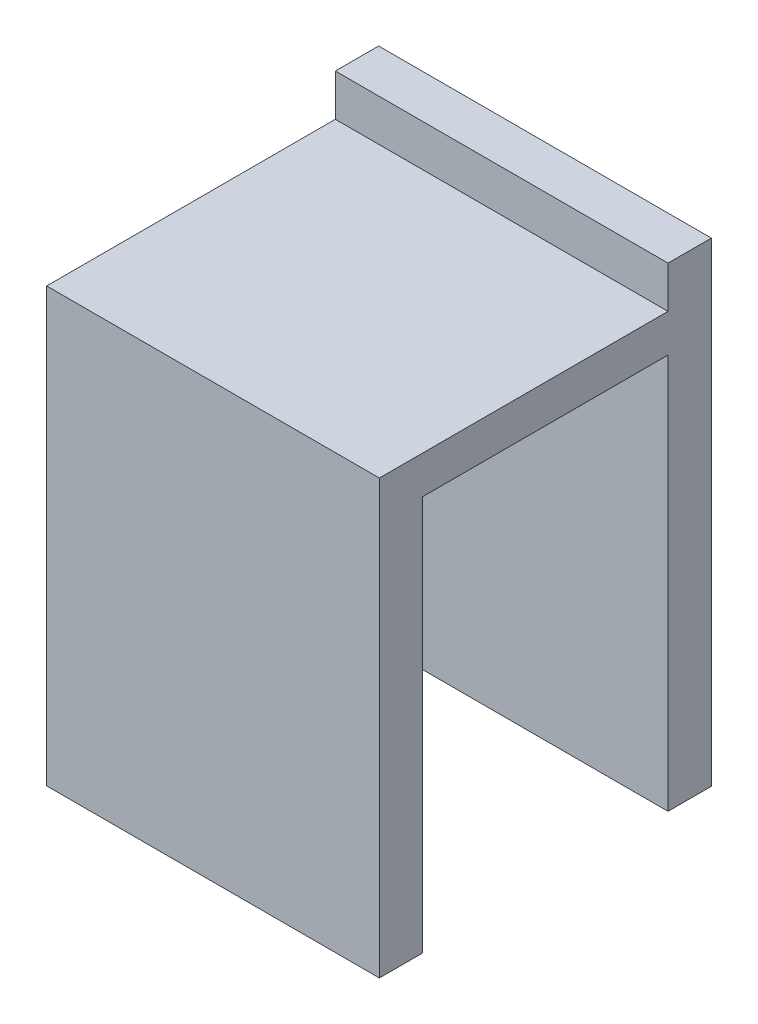
SolidWorks part; units mm, degrees
ref_plane "Front Plane" through (0, 0, 0) normal (0, 0, 1) x (1, 0, 0)
ref_plane "Top Plane" through (0, 0, 0) normal (0, 1, 0) x (1, 0, 0)
ref_plane "Right Plane" through (0, 0, 0) normal (1, 0, 0) x (0, 0, -1)
sketch "Sketch2" plane through (0, 0, -200) normal (0, 0, -1) x (-1, 0, 0)
  line L1 (91.2408, 47.6545) -> (91.2408, 22.1545) construction
  line L3 (91.2408, 22.1545) -> (91.2408, -7.8455)
  line L4 (91.2408, -7.8455) -> (68.1888, -7.8455)
  line L5 (68.1888, 22.1545) -> (68.1888, -7.8455)
  line L7 (68.1888, 22.1545) -> (68.1888, 25.0516)
  line L8 (68.1888, 25.0516) -> (91.2408, 25.0516)
  line L9 (91.2408, 22.1545) -> (91.2408, 25.0516)
  dimension "D1" = 30
extrude "Boss-Extrude1" add sketch "Sketch2" along normal blind 3
sketch "Sketch3" plane through (0, 0, -200) normal (0, 0, 1) x (1, 0, 0)
  line L0 (-91.2408, -7.8455) -> (-91.2408, 25.0516) construction
  line L1 (-91.2408, 19.5359) -> (-68.1888, 19.5359)
  line L2 (-91.2408, 19.5359) -> (-91.2408, 22.1545)
  line L3 (-91.2408, 22.1545) -> (-68.1888, 22.1545)
  line L4 (-68.1888, 19.5359) -> (-68.1888, 22.1545)
  line L5 (-68.1888, 25.0516) -> (-68.1888, -7.8455) construction
  line L6 (41.6818, 22.1545) -> (-91.2408, 22.1545) construction
extrude "Boss-Extrude2" add sketch "Sketch3" along normal blind 20
sketch "Sketch5" plane through (0, 0, -180) normal (0, 0, 1) x (1, 0, 0)
  line L1 (-91.2408, 19.5359) -> (-68.1888, 19.5359)
  line L2 (-91.2408, 19.5359) -> (-91.2408, -7.8455)
  line L3 (-91.2408, -7.8455) -> (-68.1888, -7.8455)
  line L4 (-68.1888, 19.5359) -> (-68.1888, -7.8455)
extrude "Boss-Extrude3" add sketch "Sketch5" against normal blind 3
